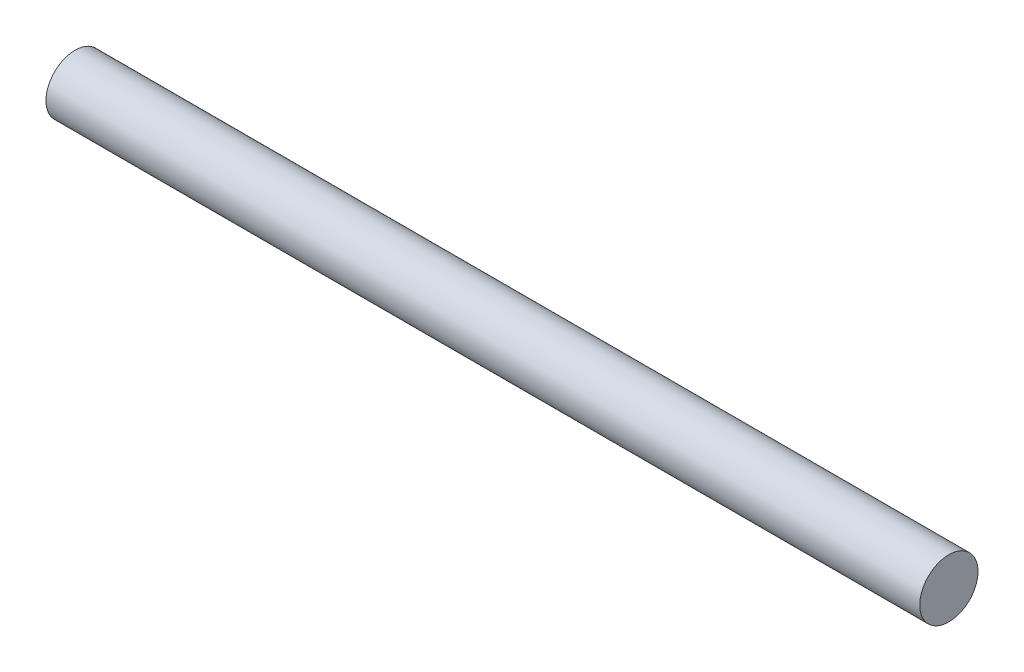
SolidWorks part; units mm, degrees
ref_plane "Płaszczyzna przednia" through (0, 0, 0) normal (0, 0, 1) x (1, 0, 0)
ref_plane "Płaszczyzna górna" through (0, 0, 0) normal (0, 1, 0) x (1, 0, 0)
ref_plane "Płaszczyzna prawa" through (0, 0, 0) normal (1, 0, 0) x (0, 0, -1)
sketch "Sketch1" plane through (0, 0, 0) normal (1, 0, 0) x (0, 0, -1)
  circle A0 centre (0, 0) radius 4
  dimension "D1" = 8
extrude "Boss-Extrude1" add sketch "Sketch1" along normal blind 120
